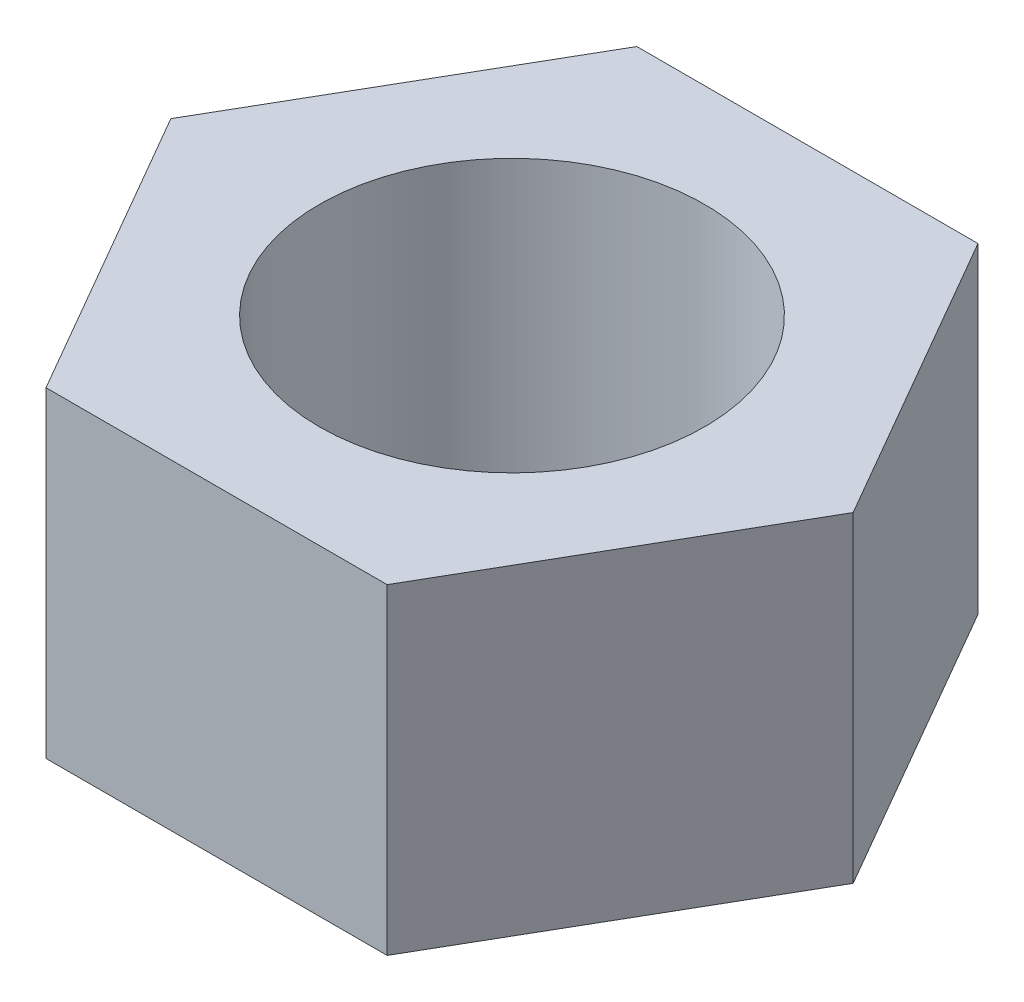
SolidWorks part; units mm, degrees
ref_plane "前视基准面" through (0, 0, 0) normal (0, 0, 1) x (1, 0, 0)
ref_plane "上视基准面" through (0, 0, 0) normal (0, 1, 0) x (1, 0, 0)
ref_plane "右视基准面" through (0, 0, 0) normal (1, 0, 0) x (0, 0, -1)
sketch "草图1" plane through (0, 0, 0) normal (0, 1, 0) x (1, 0, 0)
  line L1 (-1.3279, 2.3) -> (-2.6558, 0)
  line L2 (-2.6558, 0) -> (-1.3279, -2.3)
  line L3 (-1.3279, -2.3) -> (1.3279, -2.3)
  line L4 (1.3279, -2.3) -> (2.6558, 0)
  line L5 (2.6558, 0) -> (1.3279, 2.3)
  line L6 (1.3279, 2.3) -> (-1.3279, 2.3)
  circle A0 centre (0, 0) radius 2.3
  circle A1 centre (0, 0) radius 2.3 construction
  circle A2 centre (0, 0) radius 1.5
  dimension "D1" = 4.6
  dimension "D4" = 3
  dimension "D2" = 4.6
  dimension "D3" = 5.3116
extrude "凸台-拉伸2" add sketch "草图1" along normal blind 2.5 contours A0 A2 | A0 L6 L1 | A0 L1 L2 | A0 L5 L6 | A0 L4 L5 | A0 L3 L4 | A0 L2 L3
